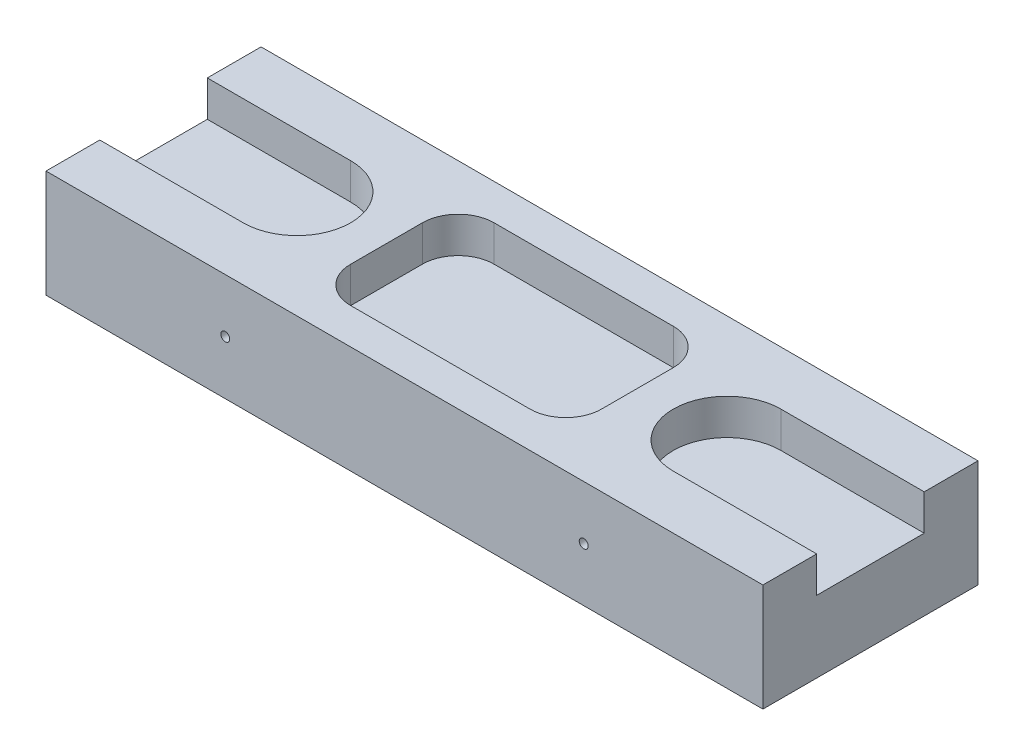
SolidWorks part; units mm, degrees
ref_plane "Front Plane" through (0, 0, 0) normal (0, 0, 1) x (1, 0, 0)
ref_plane "Top Plane" through (0, 0, 0) normal (0, 1, 0) x (1, 0, 0)
ref_plane "Right Plane" through (0, 0, 0) normal (1, 0, 0) x (0, 0, -1)
sketch "Sketch1" plane through (0, 0, 0) normal (0, 1, 0) x (1, 0, 0)
  line L1 (0, 0) -> (100, 0)
  line L2 (0, 0) -> (0, 30)
  line L3 (0, 30) -> (100, 30)
  line L4 (100, 0) -> (100, 30)
  line L7 (50, 30) -> (50, 0) construction
  dimension "D1" = 100
  dimension "D2" = 30
extrude "Boss-Extrude1" add sketch "Sketch1" along normal blind 15
sketch "Sketch2" plane through (0, 15, 0) normal (0, 1, 0) x (1, 0, 0)
  line L0 (-20, 15) -> (20, 15) construction
  line L1 (-20, 22.5) -> (20, 22.5)
  line L2 (-20, 7.5) -> (20, 7.5)
  line L3 (0, 30) -> (0, 0) construction
  line L4 (50, 30) -> (50, 0) construction
  line L5 (100, 30) -> (0, 30) construction
  line L6 (0, 0) -> (100, 0) construction
  line L7 (120, 15) -> (80, 15) construction
  line L8 (120, 22.5) -> (80, 22.5)
  line L9 (120, 7.5) -> (80, 7.5)
  arc A0 (-20, 22.5) -> (-20, 7.5) centre (-20, 15) ccw
  arc A1 (20, 7.5) -> (20, 22.5) centre (20, 15) ccw
  arc A2 (120, 22.5) -> (120, 7.5) centre (120, 15) cw
  arc A3 (80, 7.5) -> (80, 22.5) centre (80, 15) cw
  point P2 (0, 15)
  point P9 (0, 15)
  point P18 (100, 15)
  dimension "D1" = 40
  dimension "D2" = 15
extrude "Cut-Extrude1" cut sketch "Sketch2" against normal blind 5
sketch "Sketch3" plane through (0, 0, 0) normal (0, 0, 1) x (1, 0, 0)
  line L0 (0, 7.5) -> (100, 7.5) construction
  line L1 (0, 15) -> (0, 0) construction
  line L2 (100, 15) -> (100, 0) construction
  circle A0 centre (25, 7.5) radius 0.625
  circle A1 centre (75, 7.5) radius 0.625
  dimension "D1" = 1.25
  dimension "D2" = 50
  dimension "D3" = 25
extrude "Cut-Extrude2" cut sketch "Sketch3" against normal up to surface (30 mm away) up to face at (50, 7.5, -30)
sketch "Sketch4" plane through (0, 15, 0) normal (0, 1, 0) x (1, 0, 0)
  line L0 (100, 30) -> (0, 30) construction
  line L1 (37.5, 25) -> (62.5, 25)
  line L2 (32.5, 20) -> (32.5, 10)
  line L3 (37.5, 5) -> (62.5, 5)
  line L4 (67.5, 20) -> (67.5, 10)
  line L5 (0, 0) -> (100, 0) construction
  arc A0 (20, 7.5) -> (20, 22.5) centre (20, 15) ccw construction
  arc A1 (80, 22.5) -> (80, 7.5) centre (80, 15) ccw construction
  arc A2 (32.5, 10) -> (37.5, 5) centre (37.5, 10) ccw
  arc A3 (62.5, 5) -> (67.5, 10) centre (62.5, 10) ccw
  arc A4 (62.5, 25) -> (67.5, 20) centre (62.5, 20) cw
  arc A5 (37.5, 25) -> (32.5, 20) centre (37.5, 20) ccw
  point P4 (27.5, 15)
  point P5 (72.5, 15)
  dimension "D5" = 5
  dimension "D1" = 5
  dimension "D2" = 5
  dimension "D3" = 5
  dimension "D4" = 5
extrude "Cut-Extrude3" cut sketch "Sketch4" against normal blind 5
